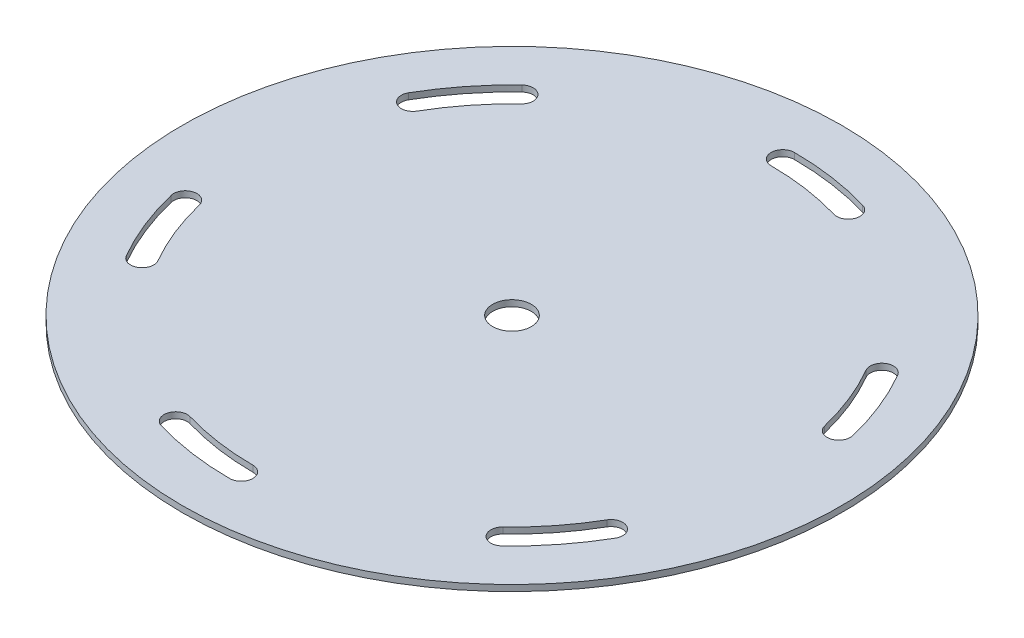
SolidWorks part; units mm, degrees
material "6061 Alloy"
ref_plane "Front Plane" through (0, 0, 0) normal (0, 0, 1) x (1, 0, 0)
ref_plane "Top Plane" through (0, 0, 0) normal (0, 1, 0) x (1, 0, 0)
ref_plane "Right Plane" through (0, 0, 0) normal (1, 0, 0) x (0, 0, -1)
sketch "Sketch1" plane through (0, 0, 0) normal (0, 1, 0) x (1, 0, 0)
  circle A0 centre (0, 0) radius 85.2
  arc A1 (60.6218, 35) -> (68.0449, 16.4286) centre (0, 0) cw construction
  arc A2 (70.9611, 17.1327) -> (63.2199, 36.5) centre (0, 0) ccw
  arc A3 (65.1286, 15.7245) -> (58.0237, 33.5) centre (0, 0) ccw
  arc A4 (65.1286, 15.7245) -> (70.9611, 17.1327) centre (68.0449, 16.4286) ccw
  arc A5 (63.2199, 36.5) -> (58.0237, 33.5) centre (60.6218, 35) ccw
  arc A6 (60.6218, -35) -> (48.25, -50.7143) centre (0, 0) cw construction
  circle A7 centre (0, 0) radius 5
  arc A8 (0, 70) -> (19.7949, 67.1429) centre (0, 0) cw construction
  arc A9 (20.6432, 70.0204) -> (0, 73) centre (0, 0) ccw
  arc A10 (18.9465, 64.2653) -> (0, 67) centre (0, 0) ccw
  arc A11 (18.9465, 64.2653) -> (20.6432, 70.0204) centre (19.7949, 67.1429) ccw
  arc A12 (0, 73) -> (0, 67) centre (0, 70) ccw
  arc A13 (50.3178, -52.8878) -> (63.2199, -36.5) centre (0, 0) ccw
  arc A14 (46.1821, -48.5408) -> (58.0237, -33.5) centre (0, 0) ccw
  arc A15 (46.1821, -48.5408) -> (50.3178, -52.8878) centre (48.25, -50.7143) ccw
  arc A16 (63.2199, -36.5) -> (58.0237, -33.5) centre (60.6218, -35) ccw
  arc A17 (0, -70) -> (-19.7949, -67.1429) centre (0, 0) cw construction
  arc A18 (-20.6432, -70.0204) -> (0, -73) centre (0, 0) ccw
  arc A19 (-18.9465, -64.2653) -> (0, -67) centre (0, 0) ccw
  arc A20 (-18.9465, -64.2653) -> (-20.6432, -70.0204) centre (-19.7949, -67.1429) ccw
  arc A21 (0, -73) -> (0, -67) centre (0, -70) ccw
  arc A22 (-60.6218, -35) -> (-68.0449, -16.4286) centre (0, 0) cw construction
  arc A23 (-70.9611, -17.1327) -> (-63.2199, -36.5) centre (0, 0) ccw
  arc A24 (-65.1286, -15.7245) -> (-58.0237, -33.5) centre (0, 0) ccw
  arc A25 (-65.1286, -15.7245) -> (-70.9611, -17.1327) centre (-68.0449, -16.4286) ccw
  arc A26 (-63.2199, -36.5) -> (-58.0237, -33.5) centre (-60.6218, -35) ccw
  arc A27 (-60.6218, 35) -> (-48.25, 50.7143) centre (0, 0) cw construction
  arc A28 (-50.3178, 52.8878) -> (-63.2199, 36.5) centre (0, 0) ccw
  arc A29 (-46.1821, 48.5408) -> (-58.0237, 33.5) centre (0, 0) ccw
  arc A30 (-46.1821, 48.5408) -> (-50.3178, 52.8878) centre (-48.25, 50.7143) ccw
  arc A31 (-63.2199, 36.5) -> (-58.0237, 33.5) centre (-60.6218, 35) ccw
  point P8 (65, 25.9808)
  point P18 (55, -43.3013)
  point P19 (10, 69.282)
  point P30 (-10, -69.282)
  point P37 (-65, -25.9808)
  point P44 (-55, 43.3013)
  point P49 (0, 0)
  dimension "D1" = 170.4
  dimension "D2" = 70
  dimension "D6" = 10
  dimension "D3" = 3
  dimension "D5" = 6
  dimension "D4" = 20
extrude "Boss-Extrude1" add sketch "Sketch1" along normal blind 1.5875
